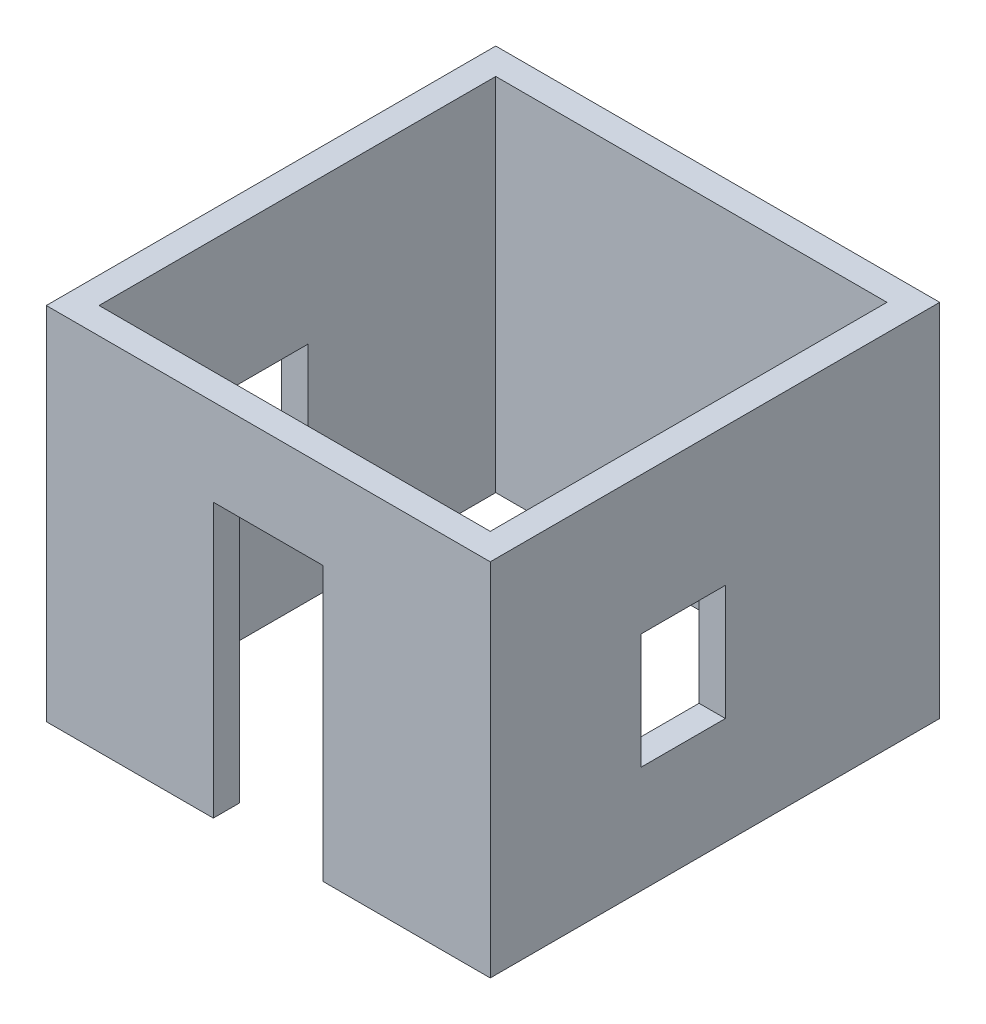
SolidWorks part; units mm, degrees
ref_plane "前视基准面" through (0, 0, 0) normal (0, 0, 1) x (1, 0, 0)
ref_plane "上视基准面" through (0, 0, 0) normal (0, 1, 0) x (1, 0, 0)
ref_plane "右视基准面" through (0, 0, 0) normal (1, 0, 0) x (0, 0, -1)
other "Configuration Table"
sketch "草图1" plane through (0, 0, 0) normal (0, 1, 0) x (1, 0, 0)
  line L1 (-1780, -1805) -> (1780, -1805)
  line L2 (-1780, -1805) -> (-1780, 1805)
  line L3 (-1780, 1805) -> (1780, 1805)
  line L4 (1780, -1805) -> (1780, 1805)
  line L5 (-1780, -1805) -> (1780, 1805) construction
  line L6 (-1780, 1805) -> (1780, -1805) construction
  point P0 (0, 0)
  dimension "D1" = 3560
  dimension "D2" = 3610
extrude "厅内壁" add sketch "草图1" along normal blind 3280 thin
sketch "草图3" plane through (0, 0, -1805) normal (0, 0, 1) x (1, 0, 0)
  line L0 (-1780, 0) -> (1780, 0) construction
  line L1 (1520, 0) -> (750, 0)
  line L2 (1520, 0) -> (1520, 1960)
  line L3 (1520, 1960) -> (750, 1960)
  line L4 (750, 0) -> (750, 1960)
  dimension "D1" = 770
  dimension "D2" = 1960
  dimension "D3" = 1030
extrude "房门" cut sketch "草图3" against normal through all
sketch "草图4" plane through (0, 0, 1805) normal (0, 0, -1) x (-1, 0, 0)
  line L1 (-500, 0) -> (500, 0)
  line L2 (-500, 0) -> (-500, 2490)
  line L3 (-500, 2490) -> (500, 2490)
  line L4 (500, 0) -> (500, 2490)
  line L6 (0, 0) -> (0, 2490) construction
  line L7 (1780, 0) -> (-1780, 0) construction
  dimension "D1" = 1000
  dimension "D2" = 2490
extrude "大门" cut sketch "草图4" against normal through all
sketch "草图5" plane through (-1780, 0, 0) normal (1, 0, 0) x (0, 0, -1)
  line L0 (-1805, 0) -> (1805, 0) construction
  line L1 (-675, 2025) -> (95, 2025)
  line L2 (-675, 2025) -> (-675, 975)
  line L3 (-675, 975) -> (95, 975)
  line L4 (95, 2025) -> (95, 975)
  line L5 (-675, 2025) -> (95, 975) construction
  line L6 (-675, 975) -> (95, 2025) construction
  point P0 (-290, 1500)
  point P7 (-675, 1500)
  dimension "D1" = 975
  dimension "D2" = 770
  dimension "D3" = 1050
  dimension "D4" = 1130
extrude "窗" cut sketch "草图5" against normal through all both and the other way through all
sketch "草图6" plane through (0, 0, 0) normal (0, 1, 0) x (1, 0, 0)
  line L0 (-1780, 1805) -> (-1780, -1805) construction
  line L5 (-1680, 1705) -> (220, 1705)
  line L6 (-1680, 1705) -> (-1680, -495)
  line L7 (-1680, -495) -> (220, -495)
  line L8 (220, 1705) -> (220, -495)
  line L9 (1780, 1805) -> (-1780, 1805) construction
  line L10 (-1780, -1805) -> (1780, -1805) construction
  line L11 (-1760, -700) -> (-1160, -700)
  line L12 (-1760, -700) -> (-1760, -1785)
  line L13 (-1760, -1785) -> (-1160, -1785)
  line L14 (-1160, -700) -> (-1160, -1785)
  line L15 (1780, 1805) -> (-1780, 1805)
  line L16 (-1780, 1805) -> (-1780, -1805)
  line L18 (-1760, -1185) -> (-675, -1185) construction
  line L19 (-1760, -1185) -> (-1760, -1785) construction
  line L20 (-1760, -1785) -> (-675, -1785) construction
  line L21 (-675, -1185) -> (-675, -1785) construction
  line L22 (-500, -2045) -> (-500, -1805) construction
  line L24 (-1680, 1705) -> (520, 1705) construction
  line L25 (-1680, 1705) -> (-1680, -195) construction
  line L26 (-1680, -195) -> (520, -195) construction
  line L27 (520, 1705) -> (520, -195) construction
  line L28 (1160, 630) -> (1760, 630)
  line L29 (1160, 630) -> (1160, -570)
  line L30 (1160, -570) -> (1760, -570)
  line L31 (1760, 630) -> (1760, -570)
  line L32 (1500, 1360) -> (1760, 1360)
  line L33 (1500, 1360) -> (1500, 680)
  line L34 (1500, 680) -> (1760, 680)
  line L35 (1760, 1360) -> (1760, 680)
  line L40 (1780, -1805) -> (1780, 1805) construction
  line L41 (1160, -620) -> (1760, -620)
  line L42 (1160, -620) -> (1160, -1705)
  line L43 (1160, -1705) -> (1760, -1705)
  line L44 (1760, -620) -> (1760, -1705)
  line L45 (500, -2045) -> (500, -1805) construction
  line L46 (750, 2045) -> (750, 1805) construction
  line L51 (-1160, -1345) -> (-505, -1345)
  line L52 (-1160, -1345) -> (-1160, -1785)
  line L53 (-1160, -1785) -> (-505, -1785)
  line L54 (-505, -1345) -> (-505, -1785)
  line L55 (505, -1345) -> (1160, -1345)
  line L56 (505, -1345) -> (505, -1785)
  line L57 (505, -1785) -> (1160, -1785)
  line L58 (1160, -1345) -> (1160, -1785)
  point P32 (1741.7424, 686.9158)
  point P51 (2556.0655, 446.7595)
  point P52 (1736.2216, -530.4282)
  dimension "D1" = 1900
  dimension "D2" = 2200
  dimension "D3" = 100
  dimension "D4" = 100
  dimension "D5" = 600
  dimension "D6" = 1085
  dimension "D7" = 20
  dimension "D8" = 20
  dimension "D9" = 205
  dimension "D10" = 3560
  dimension "D11" = 3610
  dimension "D12" = 175
  dimension "D13" = 690
  dimension "D14" = 990
  dimension "D15" = 505
  dimension "D16" = 600
  dimension "D17" = 1200
  dimension "D18" = 260
  dimension "D19" = 680
  dimension "D20" = 100
  dimension "D21" = 50
  dimension "D22" = 20
  dimension "D23" = 660
  dimension "D24" = 660
  dimension "D25" = 1280
  dimension "D26" = 655
  dimension "D27" = 440
  dimension "D28" = 20
  dimension "D29" = 20
  dimension "D30" = 50
  dimension "D31" = 445
  dimension "D32" = 940
  dimension "D33" = 850
  dimension "D34" = 530
